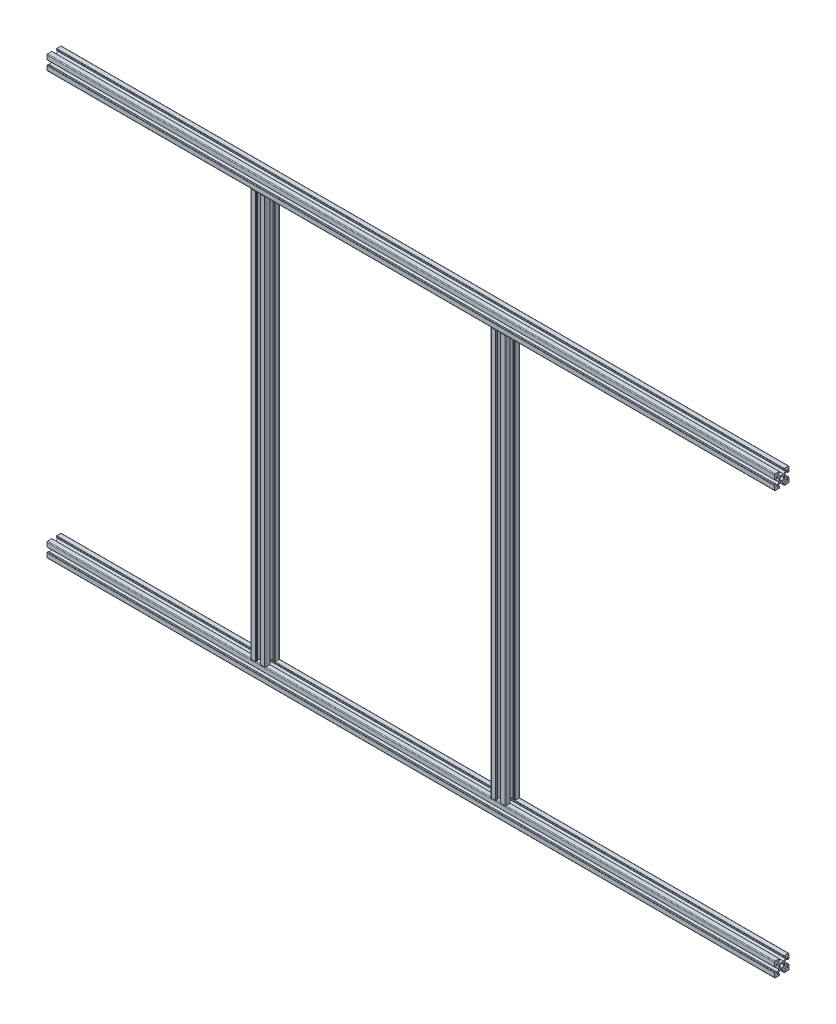
SolidWorks part; units mm, degrees
ref_plane "Front Plane" through (0, 0, 0) normal (0, 0, 1) x (1, 0, 0)
ref_plane "Top Plane" through (0, 0, 0) normal (0, 1, 0) x (1, 0, 0)
ref_plane "Right Plane" through (0, 0, 0) normal (1, 0, 0) x (0, 0, -1)
sketch "Sketch2" plane through (0, 0, 0) normal (0, 0, 1) x (1, 0, 0)
  line L0 (-437.8981, 365.0318) -> (562.1019, 365.0318)
  line L1 (-437.8981, -214.9682) -> (562.1019, -214.9682)
  line L2 (-147.8981, 365.0318) -> (-147.8981, -214.9682)
  line L3 (182.1019, 365.0318) -> (182.1019, -214.9682)
  dimension "D1" = 1000
  dimension "D2" = 1000
  dimension "D3" = 580
  dimension "D4" = 290
  dimension "D5" = 620
other "Aluminium prof ALUMINIUM PROF(1)"
ref_plane "Plane1" through (-437.8981, 365.0318, 0) normal (1, 0, 0) x (0, 1, 0)
sketch "Sketch1" plane through (-437.8981, 365.0318, 0) normal (1, 0, 0) x (0, 1, 0)
  line L0 (0, 0) -> (0, 19.0058) construction
  line L9 (0, 0) -> (23.0409, 0) construction
  line L10 (23.0409, 0) -> (23.0409, -0.0585) construction
  line L11 (23.0409, -0.0585) -> (23.0409, 0) construction
  line L13 (-2.5, 4) -> (2.5, 4)
  line L14 (2.5, 4) -> (6.0355, 7.5355)
  line L15 (6.0355, 7.5355) -> (3.5355, 7.5355)
  line L16 (3.0355, 8.0355) -> (3.0355, 9.5355)
  line L17 (3.5355, 10.0355) -> (9.0355, 10.0355)
  line L18 (10.0355, 9.0355) -> (10.0355, 3.5355)
  line L19 (9.5355, 3.0355) -> (8.0355, 3.0355)
  line L20 (7.5355, 3.5355) -> (7.5355, 6.0355)
  line L21 (7.5355, 6.0355) -> (4, 2.5)
  line L22 (4, 2.5) -> (4, -2.5)
  line L23 (-10.0355, 9.0355) -> (-10.0355, 3.5355)
  line L24 (-4, 2.5) -> (-4, -2.5)
  line L25 (-7.5355, 6.0355) -> (-4, 2.5)
  line L26 (-7.5355, 3.5355) -> (-7.5355, 6.0355)
  line L27 (-9.5355, 3.0355) -> (-8.0355, 3.0355)
  line L28 (-3.5355, 10.0355) -> (-9.0355, 10.0355)
  line L29 (-3.0355, 8.0355) -> (-3.0355, 9.5355)
  line L30 (-6.0355, 7.5355) -> (-3.5355, 7.5355)
  line L31 (-2.5, 4) -> (-6.0355, 7.5355)
  line L32 (3.5355, -10.0355) -> (9.0355, -10.0355)
  line L33 (-2.5, -4) -> (-6.0355, -7.5355)
  line L34 (-6.0355, -7.5355) -> (-3.5355, -7.5355)
  line L35 (-3.0355, -8.0355) -> (-3.0355, -9.5355)
  line L36 (-3.5355, -10.0355) -> (-9.0355, -10.0355)
  line L37 (-9.5355, -3.0355) -> (-8.0355, -3.0355)
  line L38 (-7.5355, -3.5355) -> (-7.5355, -6.0355)
  line L39 (-7.5355, -6.0355) -> (-4, -2.5)
  line L40 (-10.0355, -9.0355) -> (-10.0355, -3.5355)
  line L41 (7.5355, -6.0355) -> (4, -2.5)
  line L42 (7.5355, -3.5355) -> (7.5355, -6.0355)
  line L43 (9.5355, -3.0355) -> (8.0355, -3.0355)
  line L44 (10.0355, -9.0355) -> (10.0355, -3.5355)
  line L45 (3.0355, -8.0355) -> (3.0355, -9.5355)
  line L46 (6.0355, -7.5355) -> (3.5355, -7.5355)
  line L47 (2.5, -4) -> (6.0355, -7.5355)
  line L48 (-2.5, -4) -> (2.5, -4)
  circle A0 centre (0, 0) radius 2.5
  arc A1 (-10.0355, 9.0355) -> (-9.0355, 10.0355) centre (-9.0355, 9.0355) cw
  arc A2 (-9.0355, -10.0355) -> (-10.0355, -9.0355) centre (-9.0355, -9.0355) cw
  arc A3 (9.0355, -10.0355) -> (10.0355, -9.0355) centre (9.0355, -9.0355) ccw
  arc A4 (9.0355, 10.0355) -> (10.0355, 9.0355) centre (9.0355, 9.0355) cw
  arc A5 (-9.5355, -3.0355) -> (-10.0355, -3.5355) centre (-9.5355, -3.5355) ccw
  arc A6 (-8.0355, -3.0355) -> (-7.5355, -3.5355) centre (-8.0355, -3.5355) cw
  arc A7 (-3.5355, -7.5355) -> (-3.0355, -8.0355) centre (-3.5355, -8.0355) cw
  arc A8 (-3.0355, -9.5355) -> (-3.5355, -10.0355) centre (-3.5355, -9.5355) cw
  arc A9 (3.5355, -10.0355) -> (3.0355, -9.5355) centre (3.5355, -9.5355) cw
  arc A10 (3.0355, -8.0355) -> (3.5355, -7.5355) centre (3.5355, -8.0355) cw
  arc A11 (9.5355, -3.0355) -> (10.0355, -3.5355) centre (9.5355, -3.5355) cw
  arc A12 (7.5355, -3.5355) -> (8.0355, -3.0355) centre (8.0355, -3.5355) cw
  arc A13 (10.0355, 3.5355) -> (9.5355, 3.0355) centre (9.5355, 3.5355) cw
  arc A14 (8.0355, 3.0355) -> (7.5355, 3.5355) centre (8.0355, 3.5355) cw
  arc A15 (3.5355, 7.5355) -> (3.0355, 8.0355) centre (3.5355, 8.0355) cw
  arc A16 (3.0355, 9.5355) -> (3.5355, 10.0355) centre (3.5355, 9.5355) cw
  arc A17 (-3.5355, 10.0355) -> (-3.0355, 9.5355) centre (-3.5355, 9.5355) cw
  arc A18 (-3.0355, 8.0355) -> (-3.5355, 7.5355) centre (-3.5355, 8.0355) cw
  arc A19 (-7.5355, 3.5355) -> (-8.0355, 3.0355) centre (-8.0355, 3.5355) cw
  arc A20 (-10.0355, 3.5355) -> (-9.5355, 3.0355) centre (-9.5355, 3.5355) ccw
  point P26 (0, 4)
  point P29 (-4, 0)
  point P30 (4, 0)
  point P44 (0, -4)
  point P48 (-10.0355, 10.0355)
  point P51 (-10.0355, -10.0355)
  point P54 (10.0355, -10.0355)
  point P57 (10.0355, 10.0355)
  point P60 (-10.0355, -3.0355)
  point P63 (-7.5355, -3.0355)
  point P66 (-3.0355, -7.5355)
  point P69 (-3.0355, -10.0355)
  point P72 (3.0355, -10.0355)
  point P75 (3.0355, -7.5355)
  point P78 (10.0355, -3.0355)
  point P81 (7.5355, -3.0355)
  point P84 (10.0355, 3.0355)
  point P87 (7.5355, 3.0355)
  point P90 (3.0355, 7.5355)
  point P93 (3.0355, 10.0355)
  point P96 (-3.0355, 10.0355)
  point P99 (-3.0355, 7.5355)
  point P102 (-7.5355, 3.0355)
  point P105 (-10.0355, 3.0355)
  point P106 (0, 0)
  dimension "D5" = 4
  dimension "D12" = 1
  dimension "D13" = 0.5
  dimension "D1" = 135
  dimension "D2" = 2.5
  dimension "D3" = 4
  dimension "D4" = 2.5
  dimension "D6" = 7
  dimension "D7" = 7
  dimension "D8" = 3
  dimension "D9" = 3
  dimension "D10" = 5
  dimension "D11" = 23.0409
other "Aluminium prof ALUMINIUM PROF(2)"
ref_plane "Plane2" through (-147.8981, 365.0318, 0) normal (0, -1, 0) x (1, 0, 0)
sketch "Sketch11" plane through (-147.8981, 365.0318, 0) normal (0, -1, 0) x (1, 0, 0)
  line L0 (0, 0) -> (0, 19.0058) construction
  line L9 (0, 0) -> (23.0409, 0) construction
  line L10 (23.0409, 0) -> (23.0409, -0.0585) construction
  line L11 (23.0409, -0.0585) -> (23.0409, 0) construction
  line L13 (-2.5, 4) -> (2.5, 4)
  line L14 (2.5, 4) -> (6.0355, 7.5355)
  line L15 (6.0355, 7.5355) -> (3.5355, 7.5355)
  line L16 (3.0355, 8.0355) -> (3.0355, 9.5355)
  line L17 (3.5355, 10.0355) -> (9.0355, 10.0355)
  line L18 (10.0355, 9.0355) -> (10.0355, 3.5355)
  line L19 (9.5355, 3.0355) -> (8.0355, 3.0355)
  line L20 (7.5355, 3.5355) -> (7.5355, 6.0355)
  line L21 (7.5355, 6.0355) -> (4, 2.5)
  line L22 (4, 2.5) -> (4, -2.5)
  line L23 (-10.0355, 9.0355) -> (-10.0355, 3.5355)
  line L24 (-4, 2.5) -> (-4, -2.5)
  line L25 (-7.5355, 6.0355) -> (-4, 2.5)
  line L26 (-7.5355, 3.5355) -> (-7.5355, 6.0355)
  line L27 (-9.5355, 3.0355) -> (-8.0355, 3.0355)
  line L28 (-3.5355, 10.0355) -> (-9.0355, 10.0355)
  line L29 (-3.0355, 8.0355) -> (-3.0355, 9.5355)
  line L30 (-6.0355, 7.5355) -> (-3.5355, 7.5355)
  line L31 (-2.5, 4) -> (-6.0355, 7.5355)
  line L32 (3.5355, -10.0355) -> (9.0355, -10.0355)
  line L33 (-2.5, -4) -> (-6.0355, -7.5355)
  line L34 (-6.0355, -7.5355) -> (-3.5355, -7.5355)
  line L35 (-3.0355, -8.0355) -> (-3.0355, -9.5355)
  line L36 (-3.5355, -10.0355) -> (-9.0355, -10.0355)
  line L37 (-9.5355, -3.0355) -> (-8.0355, -3.0355)
  line L38 (-7.5355, -3.5355) -> (-7.5355, -6.0355)
  line L39 (-7.5355, -6.0355) -> (-4, -2.5)
  line L40 (-10.0355, -9.0355) -> (-10.0355, -3.5355)
  line L41 (7.5355, -6.0355) -> (4, -2.5)
  line L42 (7.5355, -3.5355) -> (7.5355, -6.0355)
  line L43 (9.5355, -3.0355) -> (8.0355, -3.0355)
  line L44 (10.0355, -9.0355) -> (10.0355, -3.5355)
  line L45 (3.0355, -8.0355) -> (3.0355, -9.5355)
  line L46 (6.0355, -7.5355) -> (3.5355, -7.5355)
  line L47 (2.5, -4) -> (6.0355, -7.5355)
  line L48 (-2.5, -4) -> (2.5, -4)
  circle A0 centre (0, 0) radius 2.5
  arc A1 (-10.0355, 9.0355) -> (-9.0355, 10.0355) centre (-9.0355, 9.0355) cw
  arc A2 (-9.0355, -10.0355) -> (-10.0355, -9.0355) centre (-9.0355, -9.0355) cw
  arc A3 (9.0355, -10.0355) -> (10.0355, -9.0355) centre (9.0355, -9.0355) ccw
  arc A4 (9.0355, 10.0355) -> (10.0355, 9.0355) centre (9.0355, 9.0355) cw
  arc A5 (-9.5355, -3.0355) -> (-10.0355, -3.5355) centre (-9.5355, -3.5355) ccw
  arc A6 (-8.0355, -3.0355) -> (-7.5355, -3.5355) centre (-8.0355, -3.5355) cw
  arc A7 (-3.5355, -7.5355) -> (-3.0355, -8.0355) centre (-3.5355, -8.0355) cw
  arc A8 (-3.0355, -9.5355) -> (-3.5355, -10.0355) centre (-3.5355, -9.5355) cw
  arc A9 (3.5355, -10.0355) -> (3.0355, -9.5355) centre (3.5355, -9.5355) cw
  arc A10 (3.0355, -8.0355) -> (3.5355, -7.5355) centre (3.5355, -8.0355) cw
  arc A11 (9.5355, -3.0355) -> (10.0355, -3.5355) centre (9.5355, -3.5355) cw
  arc A12 (7.5355, -3.5355) -> (8.0355, -3.0355) centre (8.0355, -3.5355) cw
  arc A13 (10.0355, 3.5355) -> (9.5355, 3.0355) centre (9.5355, 3.5355) cw
  arc A14 (8.0355, 3.0355) -> (7.5355, 3.5355) centre (8.0355, 3.5355) cw
  arc A15 (3.5355, 7.5355) -> (3.0355, 8.0355) centre (3.5355, 8.0355) cw
  arc A16 (3.0355, 9.5355) -> (3.5355, 10.0355) centre (3.5355, 9.5355) cw
  arc A17 (-3.5355, 10.0355) -> (-3.0355, 9.5355) centre (-3.5355, 9.5355) cw
  arc A18 (-3.0355, 8.0355) -> (-3.5355, 7.5355) centre (-3.5355, 8.0355) cw
  arc A19 (-7.5355, 3.5355) -> (-8.0355, 3.0355) centre (-8.0355, 3.5355) cw
  arc A20 (-10.0355, 3.5355) -> (-9.5355, 3.0355) centre (-9.5355, 3.5355) ccw
  point P26 (0, 4)
  point P29 (-4, 0)
  point P30 (4, 0)
  point P44 (0, -4)
  point P48 (-10.0355, 10.0355)
  point P51 (-10.0355, -10.0355)
  point P54 (10.0355, -10.0355)
  point P57 (10.0355, 10.0355)
  point P60 (-10.0355, -3.0355)
  point P63 (-7.5355, -3.0355)
  point P66 (-3.0355, -7.5355)
  point P69 (-3.0355, -10.0355)
  point P72 (3.0355, -10.0355)
  point P75 (3.0355, -7.5355)
  point P78 (10.0355, -3.0355)
  point P81 (7.5355, -3.0355)
  point P84 (10.0355, 3.0355)
  point P87 (7.5355, 3.0355)
  point P90 (3.0355, 7.5355)
  point P93 (3.0355, 10.0355)
  point P96 (-3.0355, 10.0355)
  point P99 (-3.0355, 7.5355)
  point P102 (-7.5355, 3.0355)
  point P105 (-10.0355, 3.0355)
  point P106 (0, 0)
  dimension "D5" = 4
  dimension "D12" = 1
  dimension "D13" = 0.5
  dimension "D1" = 135
  dimension "D2" = 2.5
  dimension "D3" = 4
  dimension "D4" = 2.5
  dimension "D6" = 7
  dimension "D7" = 7
  dimension "D8" = 3
  dimension "D9" = 3
  dimension "D10" = 5
  dimension "D11" = 23.0409
other "Trim/Extend1"
sketch "Sketch12" plane through (0, 0, 4) normal (0, 0, 1) x (1, 0, 0)
  line L0 (562.1019, 365.0318) -> (-437.8981, 365.0318) construction
  line L1 (562.1019, 367.5318) -> (562.1019, 362.5318) construction
  line L2 (-437.8981, 367.5318) -> (-437.8981, 362.5318) construction
  line L3 (562.1019, -214.9682) -> (-437.8981, -214.9682) construction
  line L4 (562.1019, -212.4682) -> (562.1019, -217.4682) construction
  line L5 (-437.8981, -212.4682) -> (-437.8981, -217.4682) construction
  circle A0 centre (182.1019, 365.0318) radius 2.5
  circle A1 centre (182.1019, -214.9682) radius 2.5
  dimension "D1" = 5
  dimension "D2" = 5
  dimension "D3" = 380
  dimension "D4" = 380
extrude "Cut-Extrude1" cut sketch "Sketch12" against normal blind 10
